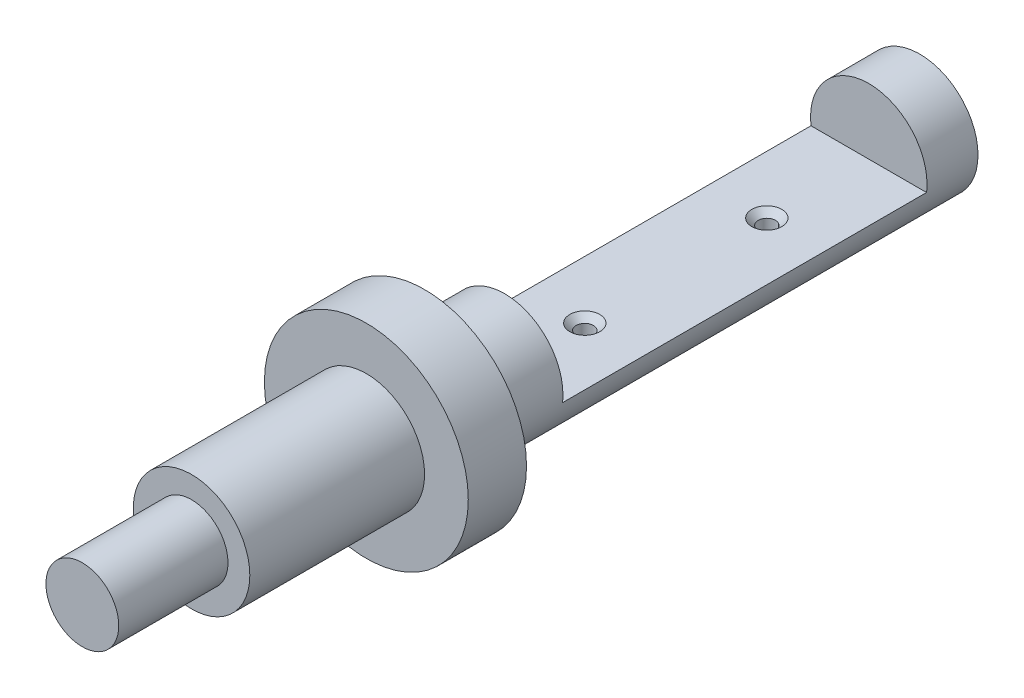
SolidWorks part; units mm, degrees
material "Plain Carbon Steel"
ref_plane "Front Plane" through (0, 0, 0) normal (0, 0, 1) x (1, 0, 0)
ref_plane "Top Plane" through (0, 0, 0) normal (0, 1, 0) x (1, 0, 0)
ref_plane "Right Plane" through (0, 0, 0) normal (1, 0, 0) x (0, 0, -1)
sketch "Sketch1" plane through (0, 0, 0) normal (0, 0, 1) x (1, 0, 0)
  circle A0 centre (0, 0) radius 8
  dimension "D1" = 16
extrude "Boss-Extrude1" add sketch "Sketch1" along normal mid plane 68
sketch "Sketch2" plane through (0, 0, 34) normal (0, 0, 1) x (1, 0, 0)
  circle A0 centre (0, 0) radius 14
  dimension "D1" = 28
extrude "Boss-Extrude2" add sketch "Sketch2" along normal blind 8
sketch "Sketch3" plane through (0, 0, 42) normal (0, 0, 1) x (1, 0, 0)
  circle A0 centre (0, 0) radius 8 construction
  circle A1 centre (0, 0) radius 8
extrude "Boss-Extrude3" add sketch "Sketch3" along normal blind 24
sketch "Sketch4" plane through (0, 0, 66) normal (0, 0, 1) x (1, 0, 0)
  circle A0 centre (0, 0) radius 5
  dimension "D1" = 10
extrude "Boss-Extrude4" add sketch "Sketch4" along normal blind 15
sketch "Sketch5" plane through (0, 0, 0) normal (1, 0, 0) x (0, 0, -1)
  line L0 (34, -8) -> (34, 8) construction
  line L1 (-23, 12.1727) -> (27, 12.1727)
  line L2 (-23, 12.1727) -> (-23, -1)
  line L3 (-23, -1) -> (27, -1)
  line L4 (27, 12.1727) -> (27, -1)
  line L5 (34, 8) -> (-34, 8) construction
  dimension "D1" = 50
  dimension "D2" = 7
  dimension "D3" = 9
extrude "Cut-Extrude1" cut sketch "Sketch5" against normal through all both and the other way through all
hole_wizard "#4-48 Tapped Hole1" positions "Sketch6" profile "Sketch7" tap size "#4-48" standard "ANSI Inch"
sketch "Sketch6" plane through (0, -1, 0) normal (0, 1, 0) x (1, 0, 0)
  line L0 (-8, 27) -> (8, 27) construction
  point P0 (0, -12)
  point P2 (0, 13)
  dimension "D1" = 25
  dimension "D2" = 14
cosmetic thread "Hole Thread1" parameters "D1"=3.05, "D2"=2.8448
cosmetic thread "Hole Thread2" parameters "D1"=3.05, "D2"=2.8448
sketch "Sketch7" plane through (0, -1, 12) normal (1, 0, 0) x (0, 0, 1)
  line L0 (0, 0) -> (0, 11.0635)
  line L1 (0, 11.0635) -> (1.1874, 10.35)
  line L2 (1.1874, 10.35) -> (1.1874, 0.87)
  line L3 (1.1874, 0.87) -> (2.0574, 0)
  line L5 (2.0574, 0) -> (0, 0)
  line L6 (-1.1874, 0.87) -> (-2.0574, 0) construction
  line L10 (0, 11.0635) -> (-1.1874, 10.35) construction
  line L11 (0, -6.35) -> (0, 107.95) construction
  dimension "Tap Drill Dia." = 2.3749
  dimension "Tap Drill Depth" = 10.35
  dimension "Near C'Sink Dia." = 4.1148
  dimension "Near C'Sink Angle" = 90
  dimension "Drill Angle" = 118
